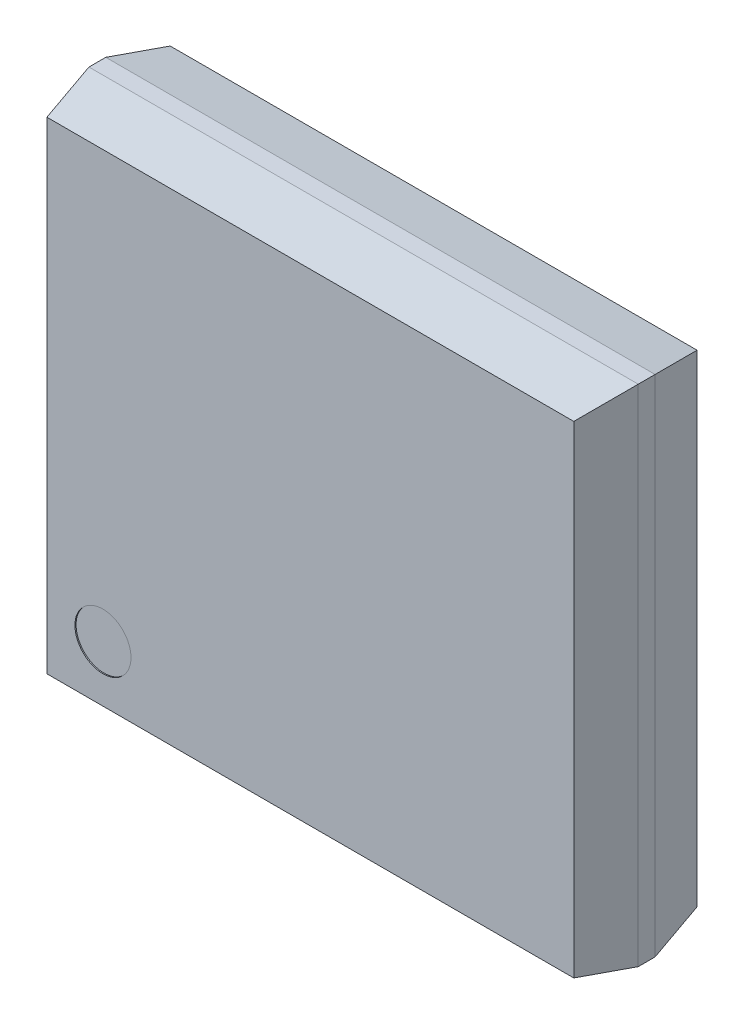
SolidWorks part; units mm, degrees
ref_plane "Front Plane" through (0, 0, 0) normal (0, 0, 1) x (1, 0, 0)
ref_plane "Top Plane" through (0, 0, 0) normal (0, 1, 0) x (1, 0, 0)
ref_plane "Right Plane" through (0, 0, 0) normal (1, 0, 0) x (0, 0, -1)
sketch "Sketch1" plane through (0, 0, 0) normal (0, 0, 1) x (1, 0, 0)
  line L1 (-2.45, -2.25) -> (2.45, -2.25)
  line L2 (-2.45, -2.25) -> (-2.45, 2.25)
  line L3 (-2.45, 2.25) -> (2.45, 2.25)
  line L4 (2.45, -2.25) -> (2.45, 2.25)
  line L5 (-2.45, -2.25) -> (2.45, 2.25) construction
  line L6 (-2.45, 2.25) -> (2.45, -2.25) construction
  point P0 (0, 0)
  dimension "D1" = 4.9
  dimension "D2" = 4.5
extrude "Boss-Extrude1" add sketch "Sketch1" along normal mid plane 1.1
sketch "Sketch2" plane through (-2.45, 0, 0) normal (-1, 0, 0) x (0, 0, 1)
  line L0 (0.55, -2.15) -> (0.075, -2.25)
  line L1 (0.55, 2.25) -> (0.55, -2.25) construction
  line L2 (0.55, -2.25) -> (-0.55, -2.25) construction
  line L3 (0.075, -2.25) -> (0.55, -2.25)
  line L4 (0.55, -2.25) -> (0.55, -2.15)
  dimension "D1" = 0.475
  dimension "D2" = 0.1
extrude "Cut-Extrude1" cut sketch "Sketch2" against normal through all
mirror "Mirror1" about plane through (0, 0, 0) normal (0, 1, 0) of "Cut-Extrude1"
mirror "Mirror2" about plane through (0, 0, 0) normal (0, 0, 1) of "Mirror1", "Cut-Extrude1"
sketch "Sketch3" plane through (0, -2.25, 0) normal (0, -1, 0) x (1, 0, 0)
  line L0 (-2.45, 0.55) -> (-2.35, 0.55)
  line L1 (2.45, 0.55) -> (-2.45, 0.55) construction
  line L2 (-2.35, 0.55) -> (-2.45, 0.075)
  line L3 (-2.45, 0.075) -> (-2.45, 0.55)
  dimension "D1" = 0.1
extrude "Cut-Extrude2" cut sketch "Sketch3" against normal through all
mirror "Mirror3" about plane through (0, 0, 0) normal (1, 0, 0) of "Cut-Extrude2"
mirror "Mirror4" about plane through (0, 0, 0) normal (0, 0, 1) of "Mirror3", "Cut-Extrude2"
sketch "Sketch4" plane through (0, 0, 0.55) normal (0, 0, 1) x (1, 0, 0)
  line L0 (2.35, -2.15) -> (-2.35, -2.15) construction
  line L1 (-2.35, 2.15) -> (-2.35, -2.15) construction
  circle A0 centre (-1.85, -1.65) radius 0.25
  dimension "D1" = 0.5
  dimension "D2" = 0.5
  dimension "D3" = 0.5
extrude "Cut-Extrude3" cut sketch "Sketch4" against normal blind 0.01
